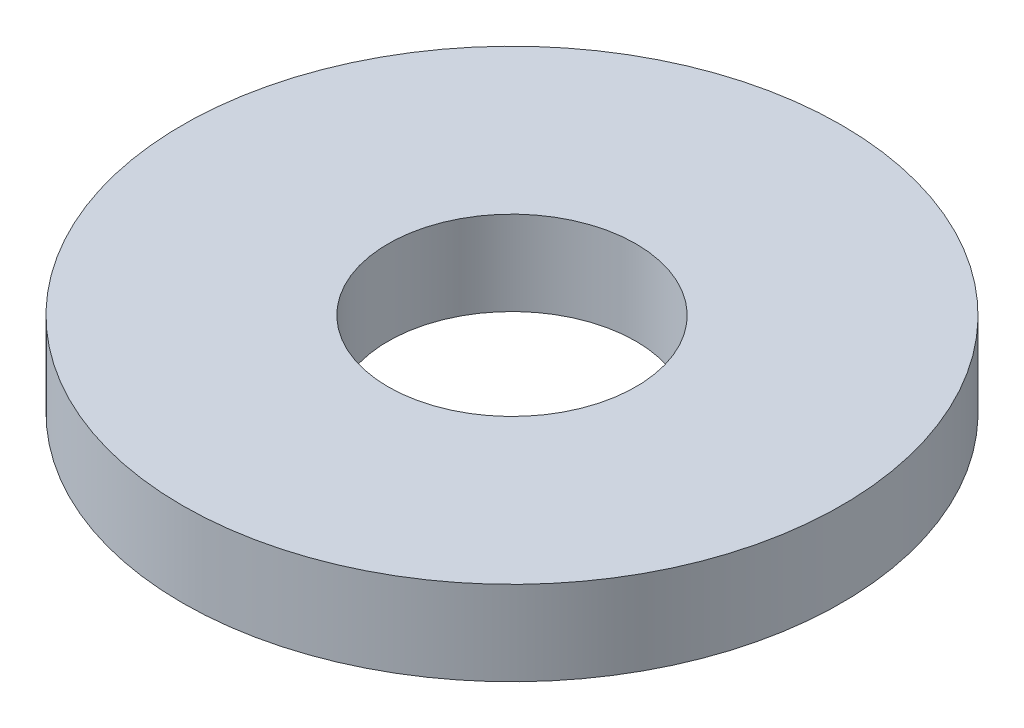
SolidWorks part; units mm, degrees
material "AISI 304"
ref_plane "Front Plane" through (0, 0, 0) normal (0, 0, 1) x (1, 0, 0)
ref_plane "Top Plane" through (0, 0, 0) normal (0, 1, 0) x (1, 0, 0)
ref_plane "Right Plane" through (0, 0, 0) normal (1, 0, 0) x (0, 0, -1)
sketch "Sketch1" plane through (0, 0, 0) normal (0, 1, 0) x (1, 0, 0)
  circle A0 centre (0, 0) radius 3.175
  dimension "OD" = 6.35
extrude "Boss-Extrude1" add sketch "Sketch1" along normal blind 0.8128
sketch "Sketch5" plane through (0, 0.8128, 0) normal (0, 1, 0) x (-1, 0, 0)
  circle A0 centre (0, 0) radius 1.1938
  dimension "ID" = 2.3876
extrude "Cut-Extrude1" cut sketch "Sketch5" against normal through all
